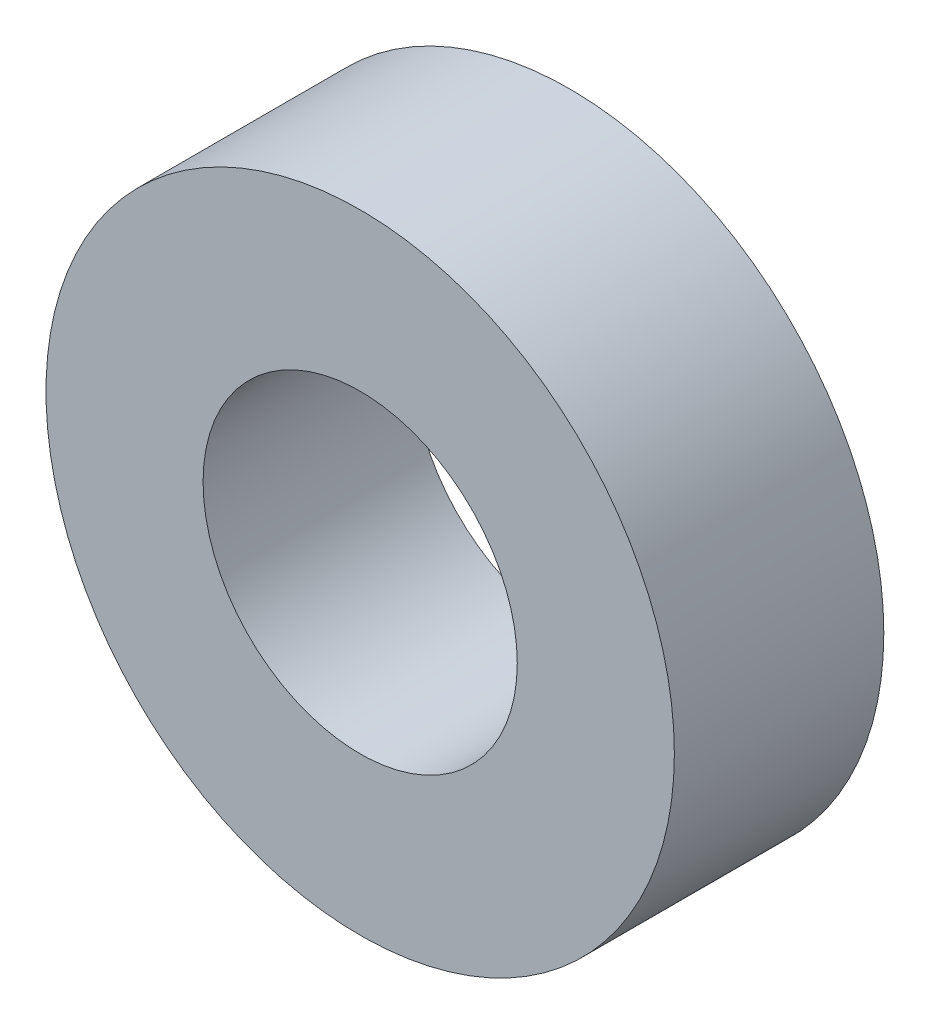
SolidWorks part; units mm, degrees
ref_plane "前视基准面" through (0, 0, 0) normal (0, 0, 1) x (1, 0, 0)
ref_plane "上视基准面" through (0, 0, 0) normal (0, 1, 0) x (1, 0, 0)
ref_plane "右视基准面" through (0, 0, 0) normal (1, 0, 0) x (0, 0, -1)
sketch "草图1" plane through (0, 0, 0) normal (0, 0, 1) x (1, 0, 0)
  circle A0 centre (0, 0) radius 3
  circle A1 centre (0, 0) radius 6
extrude "凸台-拉伸1" add sketch "草图1" along normal blind 4
